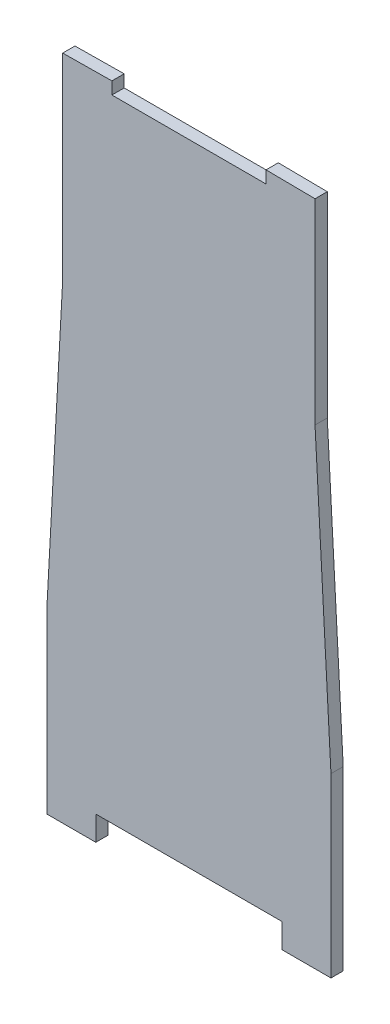
SolidWorks part; units mm, degrees
material "E-Glass Fiber"
ref_plane "Front Plane" through (0, 0, 0) normal (0, 0, 1) x (1, 0, 0)
ref_plane "Top Plane" through (0, 0, 0) normal (0, 1, 0) x (1, 0, 0)
ref_plane "Right Plane" through (0, 0, 0) normal (1, 0, 0) x (0, 0, -1)
sketch "Sketch1" plane through (0, 0, 0) normal (0, 0, 1) x (1, 0, 0)
  line L0 (0, 0) -> (0, 36.9392) construction
  line L1 (48.2546, 47.3768) -> (-48.2546, 47.3768)
  line L2 (-73.66, 50.2626) -> (-73.66, 126.4626)
  line L3 (-73.66, 126.4626) -> (-65.405, 278.8626)
  line L4 (-65.405, 278.8626) -> (-65.405, 380.4626)
  line L5 (-39.8999, 374.3842) -> (40.0064, 374.3842)
  line L6 (73.66, 50.2626) -> (73.66, 126.4626)
  line L7 (73.66, 126.4626) -> (65.405, 278.8626)
  line L8 (65.405, 278.8626) -> (65.405, 380.4626)
  line L9 (-73.66, 50.2626) -> (-73.66, 34.6768)
  line L10 (-73.66, 34.6768) -> (-48.2546, 34.6768)
  line L11 (-48.2546, 34.6768) -> (-48.2546, 47.3768)
  line L12 (73.66, 50.2626) -> (73.66, 34.7119)
  line L13 (73.66, 34.7119) -> (48.2546, 34.7119)
  line L14 (48.2546, 34.7119) -> (48.2546, 47.3768)
  line L17 (-39.8999, 380.7342) -> (-39.8999, 374.3842)
  line L20 (40.0064, 380.7356) -> (40.0064, 374.3842)
  line L21 (65.405, 380.4626) -> (40.0064, 380.7356)
  line L22 (-65.405, 380.4626) -> (-39.8999, 380.7342)
  point P12 (0, 0)
  dimension "D1" = 76.2
  dimension "D2" = 130.81
  dimension "D3" = 147.32
  dimension "D4" = 101.6
  dimension "D5" = 330.2
extrude "Boss-Extrude1" add sketch "Sketch1" along normal blind 6.35
